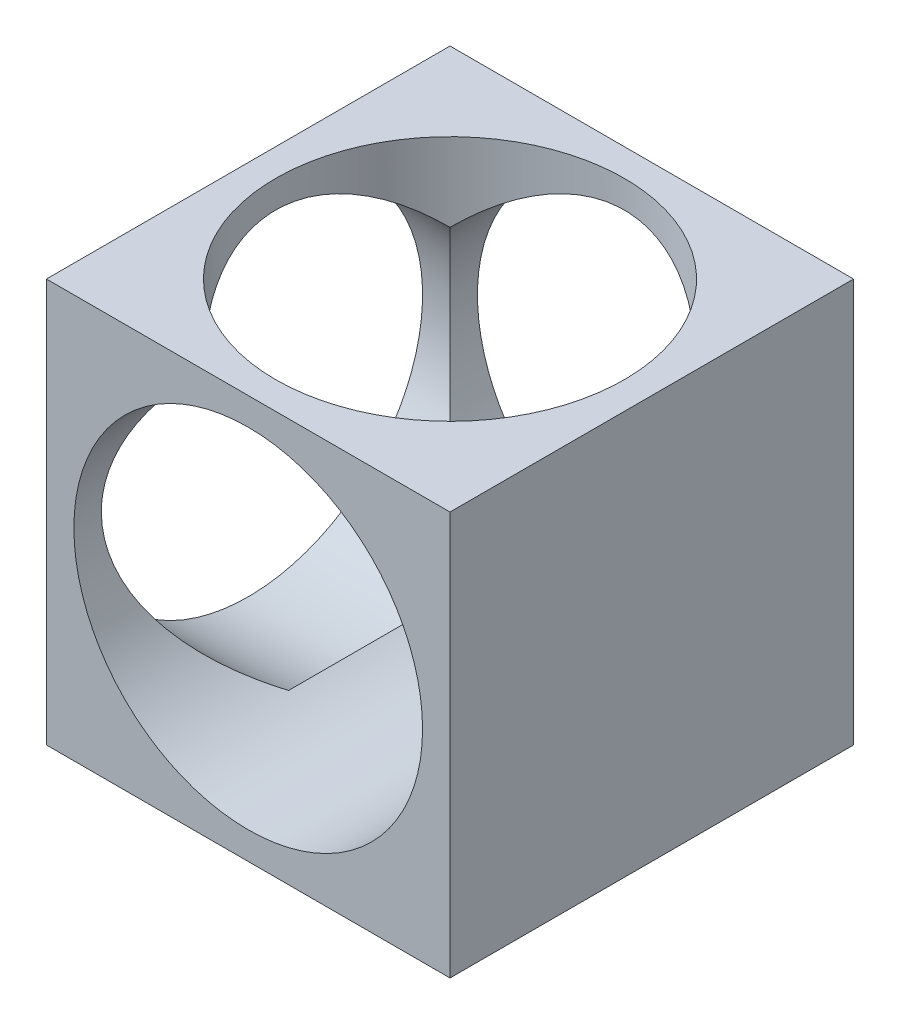
SolidWorks part; units mm, degrees
ref_plane "Front Plane" through (0, 0, 0) normal (0, 0, 1) x (1, 0, 0)
ref_plane "Top Plane" through (0, 0, 0) normal (0, 1, 0) x (1, 0, 0)
ref_plane "Right Plane" through (0, 0, 0) normal (1, 0, 0) x (0, 0, -1)
sketch "Sketch2" plane through (0, 0, 0) normal (0, 1, 0) x (1, 0, 0)
  line L1 (-15.875, -15.875) -> (15.875, -15.875)
  line L2 (-15.875, -15.875) -> (-15.875, 15.875)
  line L3 (-15.875, 15.875) -> (15.875, 15.875)
  line L4 (15.875, -15.875) -> (15.875, 15.875)
  line L5 (-15.875, -15.875) -> (15.875, 15.875) construction
  line L6 (-15.875, 15.875) -> (15.875, -15.875) construction
  point P0 (0, 0)
  dimension "D1" = 31.75
  dimension "D2" = 31.75
extrude "Boss-Extrude1" add sketch "Sketch2" along normal blind 31.75
sketch "Sketch3" plane through (0, 31.75, 0) normal (0, 1, 0) x (1, 0, 0)
  circle A0 centre (0, 0) radius 13.716
  dimension "D1" = 27.432
sketch "Sketch4" plane through (0, 0, 15.875) normal (0, 0, 1) x (1, 0, 0)
  line L0 (-15.875, 31.75) -> (-15.875, 0) construction
  circle A0 centre (0, 15.875) radius 13.716
  point P4 (-15.875, 15.875)
  dimension "D1" = 27.432
extrude "Cut-Extrude2" cut sketch "Sketch4" against normal through all both and the other way through all
sketch "Sketch5" plane through (-15.875, 0, 0) normal (-1, 0, 0) x (0, 0, 1)
  line L0 (-15.875, 31.75) -> (-15.875, 0) construction
  circle A0 centre (0, 15.875) radius 13.716
  point P4 (-15.875, 15.875)
  dimension "D1" = 27.432
extrude "Cut-Extrude3" cut sketch "Sketch5" against normal blind 9.525
extrude "Cut-Extrude4" cut sketch "Sketch3" against normal blind 7.62
